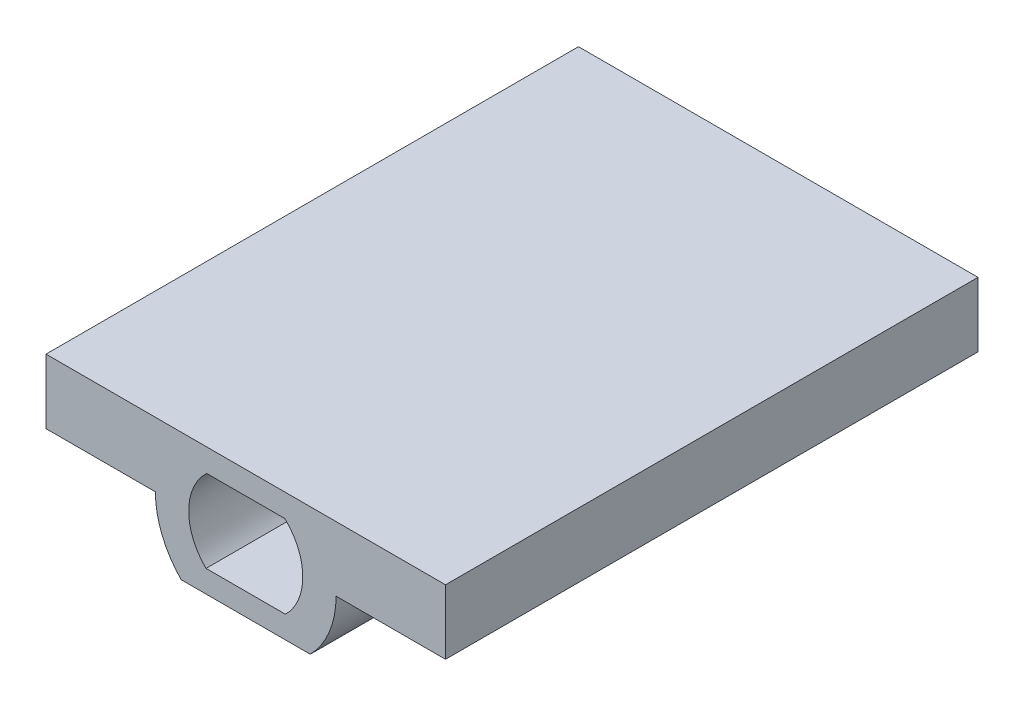
SolidWorks part; units mm, degrees
ref_plane "Front Plane" through (0, 0, 0) normal (0, 0, 1) x (1, 0, 0)
ref_plane "Top Plane" through (0, 0, 0) normal (0, 1, 0) x (1, 0, 0)
ref_plane "Right Plane" through (0, 0, 0) normal (1, 0, 0) x (0, 0, -1)
sketch "Sketch1" plane through (0, 0, 0) normal (0, 0, 1) x (1, 0, 0)
  line L4 (-38.1093, 0) -> (-38.1093, 12.319)
  line L6 (38.1172, 12.319) -> (38.1172, 0)
  line L10 (-7.4595, 7.9315) -> (7.4595, 7.9315)
  line L11 (-7.5755, -7.8208) -> (7.5755, -7.8208)
  line L14 (-38.1093, 12.319) -> (38.1172, 12.319)
  line L16 (-38.1093, 0) -> (-17.2382, 0)
  line L17 (17.2382, 0) -> (38.1172, 0)
  line L18 (-9.8156, -14.1708) -> (9.8156, -14.1708) construction
  line L19 (-9.6537, 14.2815) -> (9.6537, 14.2815) construction
  line L20 (-12.0581, -12.065) -> (12.0581, -12.065)
  line L21 (-12.0581, -12.065) -> (-12.3123, -12.065)
  line L22 (12.0581, -12.065) -> (12.3123, -12.065)
  arc A2 (7.5755, -7.8208) -> (7.4595, 7.9315) centre (0, 0) ccw
  arc A3 (-7.4595, 7.9315) -> (-7.5755, -7.8208) centre (0, 0) ccw
  arc A4 (12.3123, -12.065) -> (17.2382, 0) centre (0, 0) ccw
  arc A5 (-17.2382, 0) -> (-12.3123, -12.065) centre (0, 0) ccw
  arc A6 (-9.6537, 14.2815) -> (-9.8156, -14.1708) centre (0, 0) ccw construction
  arc A7 (9.8156, -14.1708) -> (9.6537, 14.2815) centre (0, 0) ccw construction
  dimension "D1" = 6.35
extrude "Boss-Extrude1" add sketch "Sketch1" against normal blind 101.6
